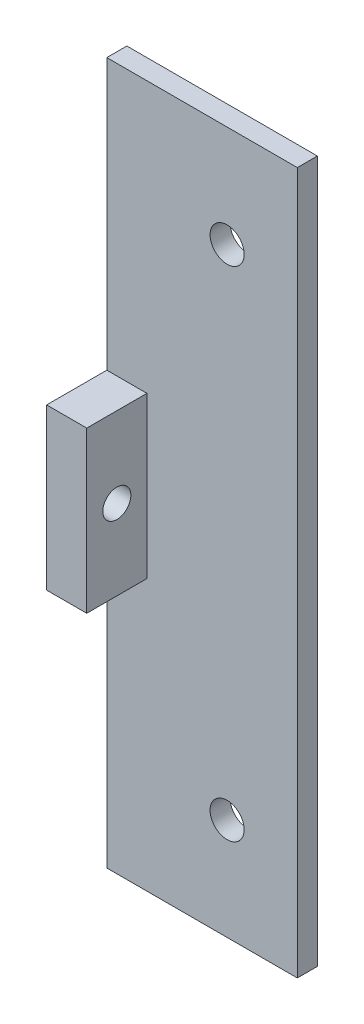
SolidWorks part; units mm, degrees
ref_plane "Plan de face" through (0, 0, 0) normal (0, 0, 1) x (1, 0, 0)
ref_plane "Plan de dessus" through (0, 0, 0) normal (0, 1, 0) x (1, 0, 0)
ref_plane "Plan de droite" through (0, 0, 0) normal (1, 0, 0) x (0, 0, -1)
sketch "Esquisse1" plane through (0, 0, 0) normal (0, 0, 1) x (1, 0, 0)
  line L0 (7, 10.15) -> (7, -59.85)
  line L1 (0, 0) -> (0, -49.7) construction
  line L2 (7, -24.85) -> (-3.4703, -24.85) construction
  line L3 (0, -24.85) -> (-8.0205, -24.85) construction
  line L4 (-12, 10.15) -> (-12, -59.85) construction
  line L5 (7, 10.15) -> (-12, 10.15)
  line L6 (-12, 10.15) -> (-12, -59.85)
  line L7 (-12, -59.85) -> (7, -59.85)
  circle A0 centre (0, 0) radius 1.7
  circle A1 centre (0, -49.7) radius 1.7
  dimension "D1" = 49.7
  dimension "D2" = 7
  dimension "D3" = 70
  dimension "D4" = 0
  dimension "D5" = 12
extrude "Boss.-Extru.1" add sketch "Esquisse1" along normal blind 2
sketch "Esquisse2" plane through (-12, 0, 0) normal (-1, 0, 0) x (0, 0, 1)
  line L0 (2, -24.85) -> (0, -24.85) construction
  line L1 (2, 10.15) -> (2, -59.85) construction
  line L2 (0, 10.15) -> (0, -59.85) construction
  line L3 (0, -32.85) -> (8, -32.85) construction
  line L4 (8, -32.85) -> (8, -24.85) construction
  line L5 (8, -24.85) -> (2, -24.85) construction
  line L6 (4, -32.85) -> (4, -24.85) construction
  line L7 (2, -32.85) -> (2, -24.85) construction
  line L8 (0, -16.85) -> (0, -32.85)
  line L9 (0, -32.85) -> (8, -32.85)
  line L10 (8, -32.85) -> (8, -16.85)
  line L11 (0, -16.85) -> (8, -16.85)
  dimension "D1" = 8
  dimension "D2" = 2
  dimension "D3" = 8
extrude "Boss.-Extru.2" add sketch "Esquisse2" against normal blind 4
sketch "Esquisse3" plane through (-12, 0, 0) normal (-1, 0, 0) x (0, 0, 1)
  line L0 (5, -32.85) -> (5, -16.85) construction
  line L1 (2, -32.85) -> (8, -32.85) construction
  line L2 (8, -16.85) -> (2, -16.85) construction
  line L3 (8, -24.85) -> (0, -24.85) construction
  line L4 (8, -32.85) -> (8, -16.85) construction
  line L5 (0, 10.15) -> (0, -59.85) construction
  circle A0 centre (5, -24.85) radius 1.4
extrude "Enlèv. mat.-Extru.1" cut sketch "Esquisse3" against normal blind 4
